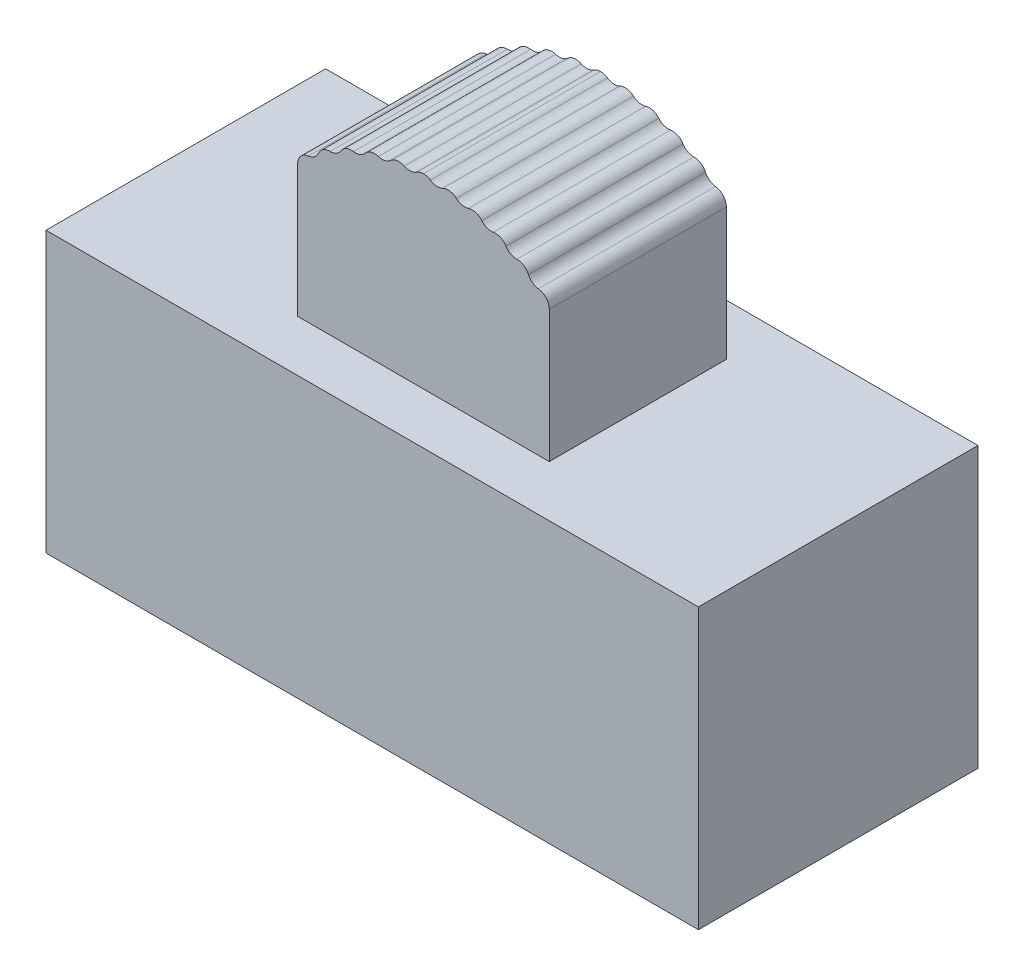
SolidWorks part; units mm, degrees
ref_plane "Front Plane" through (0, 0, 0) normal (0, 0, 1) x (1, 0, 0)
ref_plane "Top Plane" through (0, 0, 0) normal (0, 1, 0) x (1, 0, 0)
ref_plane "Right Plane" through (0, 0, 0) normal (1, 0, 0) x (0, 0, -1)
sketch "Sketch1" plane through (0, 0, 0) normal (0, 1, 0) x (1, 0, 0)
  line L0 (-7, 0) -> (7, 0) construction
  line L1 (-7, 3) -> (7, 3)
  line L2 (-7, 3) -> (-7, -3)
  line L3 (-7, -3) -> (7, -3)
  line L4 (7, 3) -> (7, -3)
  point P6 (0, 0)
  dimension "D1" = 14
  dimension "D2" = 6
extrude "Boss-Extrude1" add sketch "Sketch1" along normal blind 6
sketch "Sketch2" plane through (0, 6, 0) normal (0, 1, 0) x (1, 0, 0)
  line L0 (-2.7, 0) -> (2.7, 0) construction
  line L1 (-2.7, 1.9) -> (2.7, 1.9)
  line L2 (-2.7, 1.9) -> (-2.7, -1.9)
  line L3 (-2.7, -1.9) -> (2.7, -1.9)
  line L4 (2.7, 1.9) -> (2.7, -1.9)
  point P6 (0, 0)
  dimension "D1" = 5.4
  dimension "D2" = 3.8
extrude "Boss-Extrude2" add sketch "Sketch2" along normal blind 4
sketch "Sketch3" plane through (0, 0, 1.9) normal (0, 0, 1) x (1, 0, 0)
  line L0 (-2.7, 6) -> (2.7, 6) construction
  line L1 (-2.7, 10) -> (-2.7, 6) construction
  line L2 (-2.7, 8.8321) -> (-2.7, 10)
  line L3 (-2.7, 10) -> (2.7, 10) construction
  line L4 (0, 6) -> (0, 6.0962) construction
  line L5 (0, 10) -> (0, 6) construction
  line L6 (2.7, 8.8321) -> (2.7, 10)
  line L7 (2.7, 10) -> (-2.7, 10)
  circle A0 centre (0, 6) radius 4 construction
  arc A1 (-2.4655, 9.0954) -> (-2.7, 8.8321) centre (-2.435, 8.8321) ccw
  arc A2 (-2.0026, 9.4132) -> (-2.2529, 9.2534) centre (-2.0096, 9.1483) ccw
  arc A3 (-1.4993, 9.6623) -> (-1.7697, 9.5396) centre (-1.5438, 9.401) ccw
  arc A4 (-2.4655, 9.0954) -> (-2.2529, 9.2534) centre (-2.4961, 9.3586) ccw
  arc A5 (-2.0026, 9.4132) -> (-1.7697, 9.5396) centre (-1.9956, 9.6781) ccw
  arc A6 (-1.4993, 9.6623) -> (-1.2509, 9.7544) centre (-1.4549, 9.9235) ccw
  arc A7 (-0.9659, 9.8376) -> (-1.2509, 9.7544) centre (-1.0468, 9.5853) ccw
  arc A8 (-0.4129, 9.9357) -> (-0.7068, 9.8937) centre (-0.5288, 9.6974) ccw
  arc A9 (-0.0002, 10) -> (-0.1486, 9.9545) centre (-0.0002, 9.735) ccw
  arc A10 (-0.9659, 9.8376) -> (-0.7068, 9.8937) centre (-0.8849, 10.09) ccw
  arc A11 (-0.4129, 9.9357) -> (-0.1486, 9.9545) centre (-0.2971, 10.174) ccw
  arc A12 (1.4993, 9.6623) -> (1.7697, 9.5396) centre (1.5438, 9.401) cw
  arc A13 (2.0026, 9.4132) -> (1.7697, 9.5396) centre (1.9956, 9.6781) cw
  arc A14 (2.0026, 9.4132) -> (2.2529, 9.2534) centre (2.0096, 9.1483) cw
  arc A15 (2.4655, 9.0954) -> (2.2529, 9.2534) centre (2.4961, 9.3586) cw
  arc A16 (2.4655, 9.0954) -> (2.7, 8.8321) centre (2.435, 8.8321) cw
  arc A17 (1.4993, 9.6623) -> (1.2509, 9.7544) centre (1.4549, 9.9235) cw
  arc A18 (0.9659, 9.8376) -> (1.2509, 9.7544) centre (1.0468, 9.5853) cw
  arc A19 (0.9659, 9.8376) -> (0.7068, 9.8937) centre (0.8849, 10.09) cw
  arc A20 (0.4129, 9.9357) -> (0.7068, 9.8937) centre (0.5288, 9.6974) cw
  arc A21 (0.4129, 9.9357) -> (0.1486, 9.9545) centre (0.2971, 10.174) cw
  arc A22 (0.0002, 10) -> (0.1486, 9.9545) centre (0.0002, 9.735) cw
  line M3 (2.7, 6) -> (2.7, 10)
  line M4 (2.7, 10) -> (-2.7, 10)
  line M5 (-2.7, 10) -> (-2.7, 6)
  dimension "D1" = 0.53
extrude "Cut-Extrude1" cut sketch "Sketch3" against normal through all contours A8 A11 A9 L7 A1 A4 A2 A5 A3 A6 A7 A10 M5 | A22 A21 A20 A19 A18 A17 A12 A13 A14 A15 A16 M4 M3
